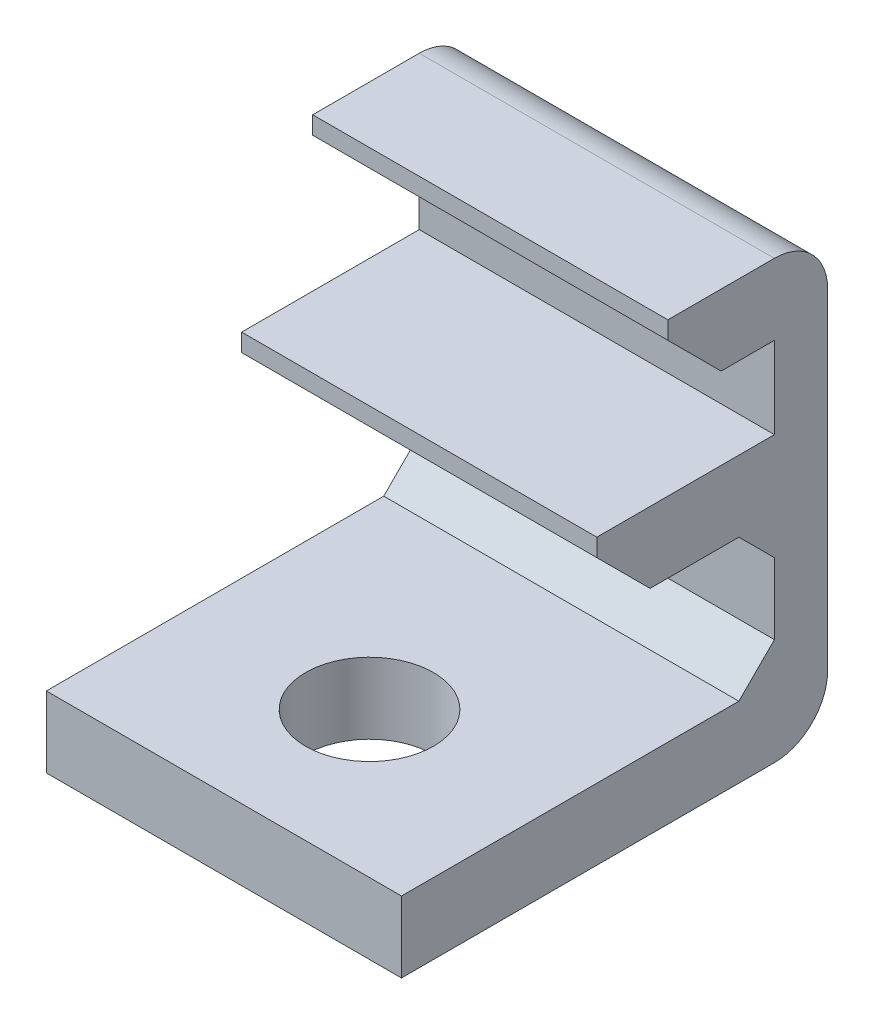
SolidWorks part; units mm, degrees
ref_plane "Plano frontal" through (0, 0, 0) normal (0, 0, 1) x (1, 0, 0)
ref_plane "Plano superior" through (0, 0, 0) normal (0, 1, 0) x (1, 0, 0)
ref_plane "Plano direito" through (0, 0, 0) normal (1, 0, 0) x (0, 0, -1)
sketch "Sketch1" plane through (0, 0, 0) normal (1, 0, 0) x (0, 0, -1)
  line L0 (-5.25, -4.15) -> (-5.25, -6.15)
  line L1 (2.25, 6.15) -> (6.75, 6.15)
  line L2 (2.25, 6.15) -> (2.25, 4.15)
  line L3 (-5.25, -6.15) -> (6.75, -6.15)
  line L4 (6.75, 6.15) -> (6.75, -6.15)
  line L5 (2.25, 4.15) -> (5.25, 4.15)
  line L7 (-5.25, -4.15) -> (5.25, -4.15)
  line L8 (5.25, 4.15) -> (5.25, 1.85)
  line L9 (5.25, -0.15) -> (5.25, -4.15)
  line L10 (0.25, 1.85) -> (5.25, 1.85)
  line L11 (0.25, 1.85) -> (0.25, -0.15)
  line L12 (0.25, -0.15) -> (5.25, -0.15)
  point P7 (6.75, 0)
  point P15 (0, -4.15)
  dimension "D1" = 8
  dimension "D2" = 4.5
  dimension "D3" = 1.5
  dimension "D4" = 2
  dimension "D5" = 2.3
  dimension "D6" = 12
  dimension "D7" = 5
  dimension "D8" = 4
  dimension "D9" = 10.3
extrude "Boss-Extrude1" add sketch "Sketch1" along normal mid plane 10 contours L5 L8 L7 L2 L3 L4 L1
chamfer "Chamfer1" distance 1 angle 45 2 edges at (0, -0.15, -5.25) (0, -4.15, -5.25)
sketch "Sketch2" plane through (0, -4.15, 0) normal (0, 1, 0) x (1, 0, 0)
  line L2 (5, -5.25) -> (-5, -5.25) construction
  circle A0 centre (0, -1.15) radius 1.5 construction
  circle A1 centre (0, -1.15) radius 1.8
  dimension "D1" = 3
  dimension "D3" = 2.3
  dimension "D2" = 0.3
extrude "Cut-Extrude1" cut sketch "Sketch2" against normal through all and the other way blind 3
fillet "Fillet1" radius 1.5 2 edges at (0, -6.15, -6.75) (0, 6.15, -6.75)
chamfer "Chamfer2" distance 1.5 angle 45 2 edges at (0, 4.15, -2.25) (0, -0.15, -0.25)
